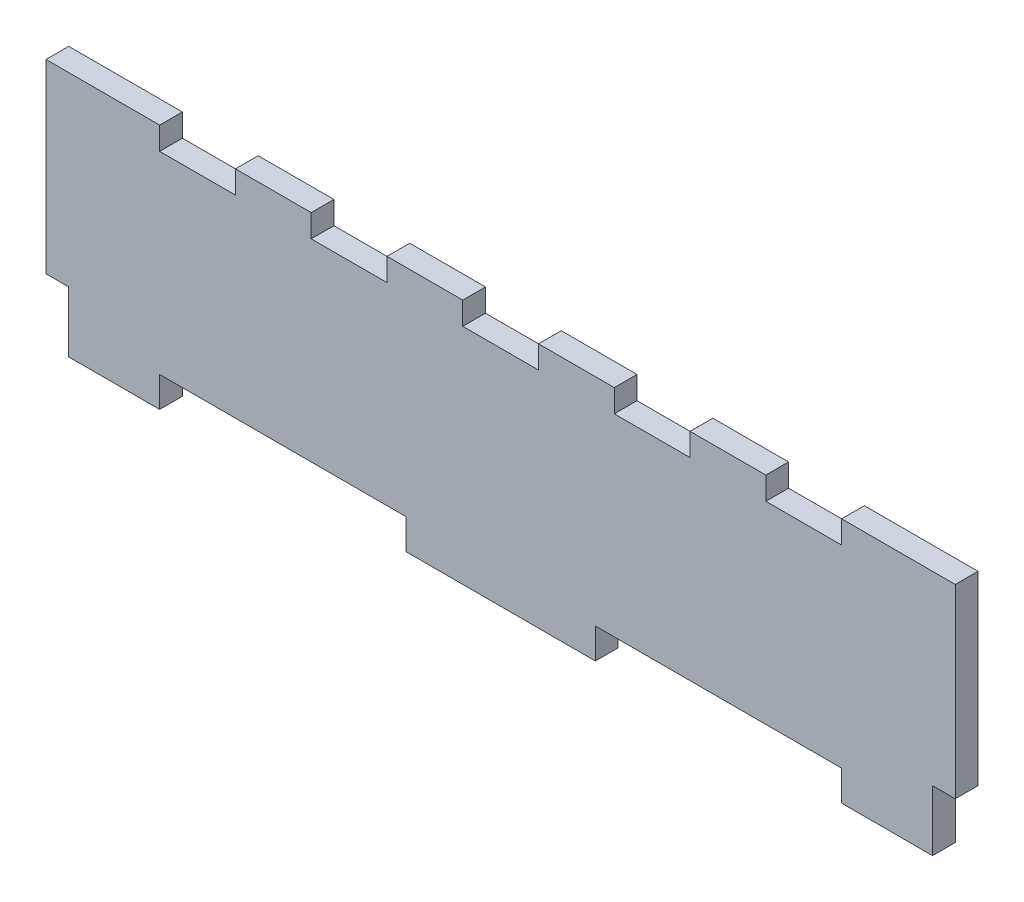
SolidWorks part; units mm, degrees
ref_plane "Front Plane" through (0, 0, 0) normal (0, 0, 1) x (1, 0, 0)
ref_plane "Top Plane" through (0, 0, 0) normal (0, 1, 0) x (1, 0, 0)
ref_plane "Right Plane" through (0, 0, 0) normal (1, 0, 0) x (0, 0, -1)
sketch "Sketch1" plane through (0, 0, 0) normal (0, 0, 1) x (1, 0, 0)
  line L1 (-120, -32.5) -> (120, -32.5)
  line L2 (-120, -32.5) -> (-120, 32.5)
  line L3 (-120, 32.5) -> (120, 32.5)
  line L4 (120, -32.5) -> (120, 32.5)
  line L5 (-120, -32.5) -> (120, 32.5) construction
  line L6 (-120, 32.5) -> (120, -32.5) construction
  point P0 (0, 0)
  dimension "D1" = 65
  dimension "D2" = 240
extrude "Boss-Extrude1" add sketch "Sketch1" along normal mid plane 6
sketch "Sketch2" plane through (0, 0, 3) normal (0, 0, 1) x (1, 0, 0)
  line L0 (-120, -32.5) -> (120, -32.5) construction
  line L1 (-120, -32.5) -> (-114, -32.5)
  line L2 (-120, -32.5) -> (-120, -16.5)
  line L3 (-120, -16.5) -> (-114, -16.5)
  line L4 (-114, -32.5) -> (-114, -16.5)
  line L5 (-90, -32.5) -> (-25, -32.5)
  line L6 (-90, -32.5) -> (-90, -24.5)
  line L7 (-90, -24.5) -> (-25, -24.5)
  line L8 (-25, -32.5) -> (-25, -24.5)
  line L9 (0, 32.5) -> (0, -32.5) construction
  line L10 (120, 32.5) -> (-120, 32.5) construction
  line L11 (25, -32.5) -> (25, -24.5)
  line L12 (90, -24.5) -> (25, -24.5)
  line L13 (90, -32.5) -> (90, -24.5)
  line L14 (90, -32.5) -> (25, -32.5)
  line L15 (114, -32.5) -> (114, -16.5)
  line L16 (120, -16.5) -> (114, -16.5)
  line L17 (120, -32.5) -> (120, -16.5)
  line L18 (120, -32.5) -> (114, -32.5)
  dimension "D1" = 6
  dimension "D2" = 16
  dimension "D3" = 8
  dimension "D4" = 65
  dimension "D5" = 24
extrude "Cut-Extrude1" cut sketch "Sketch2" against normal up to surface (6 mm away) up to face at (0, 0, -3)
sketch "Sketch3" plane through (0, 0, 3) normal (0, 0, 1) x (1, 0, 0)
  line L0 (120, 32.5) -> (-120, 32.5) construction
  line L1 (-90, 32.5) -> (-70, 32.5)
  line L2 (-90, 32.5) -> (-90, 26.5)
  line L3 (-90, 26.5) -> (-70, 26.5)
  line L4 (-70, 32.5) -> (-70, 26.5)
  line L5 (-50, 32.5) -> (-30, 32.5)
  line L6 (-50, 32.5) -> (-50, 26.5)
  line L7 (-50, 26.5) -> (-30, 26.5)
  line L8 (-30, 32.5) -> (-30, 26.5)
  line L9 (-10, 32.5) -> (10, 32.5)
  line L10 (-10, 32.5) -> (-10, 26.5)
  line L11 (-10, 26.5) -> (10, 26.5)
  line L12 (10, 32.5) -> (10, 26.5)
  line L13 (30, 32.5) -> (50, 32.5)
  line L14 (30, 32.5) -> (30, 26.5)
  line L15 (30, 26.5) -> (50, 26.5)
  line L16 (50, 32.5) -> (50, 26.5)
  line L17 (70, 32.5) -> (90, 32.5)
  line L18 (70, 32.5) -> (70, 26.5)
  line L19 (70, 26.5) -> (90, 26.5)
  line L20 (90, 32.5) -> (90, 26.5)
  dimension "D1" = 6
  dimension "D2" = 30
  dimension "D3" = 20
  dimension "D4" = 5
extrude "Cut-Extrude2" cut sketch "Sketch3" against normal up to surface (6 mm away) up to face at (0, -18.375, -3)
equation "\"Material Thickness\"=6"
equation "\"D1@Boss-Extrude1\"=\"Material Thickness\""
equation "\"D2@Sketch2\"=\"Material Thickness\"+10"
equation "\"D3@Sketch2\"=\"Material Thickness\"+2"
equation "\"D1@Sketch2\"=\"Material Thickness\""
equation "\"D1@Sketch3\"=\"Material Thickness\""
